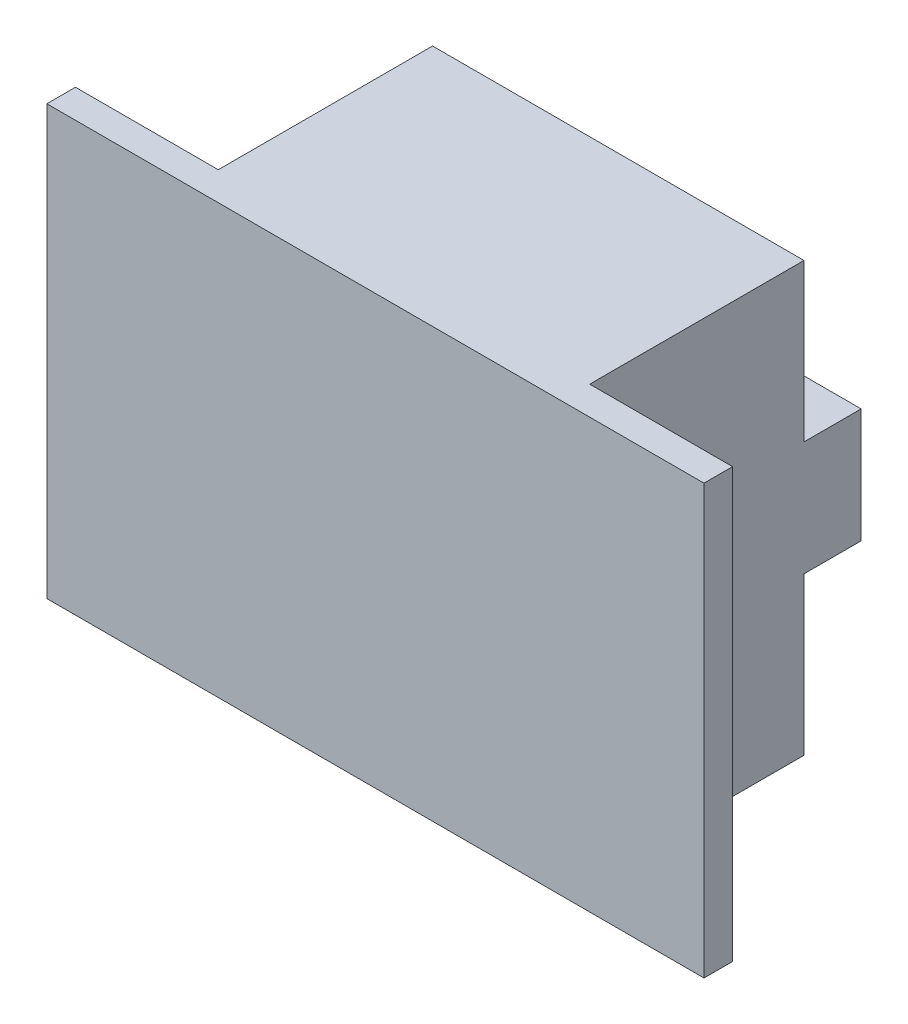
SolidWorks part; units mm, degrees
ref_plane "前视基准面" through (0, 0, 0) normal (0, 0, 1) x (1, 0, 0)
ref_plane "上视基准面" through (0, 0, 0) normal (0, 1, 0) x (1, 0, 0)
ref_plane "右视基准面" through (0, 0, 0) normal (1, 0, 0) x (0, 0, -1)
other "Configuration Table"
sketch "草图1" plane through (0, 0, 0) normal (0, 0, 1) x (1, 0, 0)
  line L0 (-447, 865) -> (-447, -15) construction
  line L1 (-473, 865) -> (-473, -15) construction
  line L2 (-447, 865) -> (-447, -15) construction
  line L3 (-473, 865) -> (-473, -15) construction
  line L4 (-473, -15) -> (-447, -15)
  line L5 (-447, -15) -> (-447, 15)
  line L6 (-447, 15) -> (-473, 15)
  line L7 (-473, 15) -> (-473, -15)
  dimension "D1" = 30
extrude "凸台-拉伸1" add sketch "草图1" along normal blind 15
sketch "草图2" plane through (0, 0, 15) normal (0, 0, 1) x (1, 0, 0)
  line L1 (-483, -15) -> (-437, -15)
  line L2 (-473, -15) -> (-447, -15) construction
  line L3 (-483, 15) -> (-437, 15)
  line L4 (-447, 15) -> (-473, 15) construction
  line L5 (-483, -15) -> (-483, 15)
  line L6 (-437, -15) -> (-437, 15)
  line L7 (-473, 15) -> (-473, -15) construction
  line L9 (-447, -15) -> (-447, 15) construction
  point P9 (-461.7784, 15)
  dimension "D1" = 10
  dimension "D2" = 10
extrude "凸台-拉伸2" add sketch "草图2" along normal blind 2
sketch "草图4" plane through (0, 0, 0) normal (0, 0, -1) x (-1, 0, 0)
  line L0 (447, 0) -> (473, 0) construction
  line L1 (447, -15) -> (447, 15) construction
  line L2 (473, 15) -> (473, -15) construction
  line L3 (447, -4) -> (473, -4)
  line L4 (447, -15) -> (447, 15) construction
  line L5 (473, 15) -> (473, -15) construction
  line L6 (473, -4) -> (473, 4)
  line L7 (473, 4) -> (447, 4)
  line L8 (447, 4) -> (447, -4)
  dimension "D1" = 4
  dimension "D2" = 4
extrude "凸台-拉伸3" add sketch "草图4" along normal blind 4
